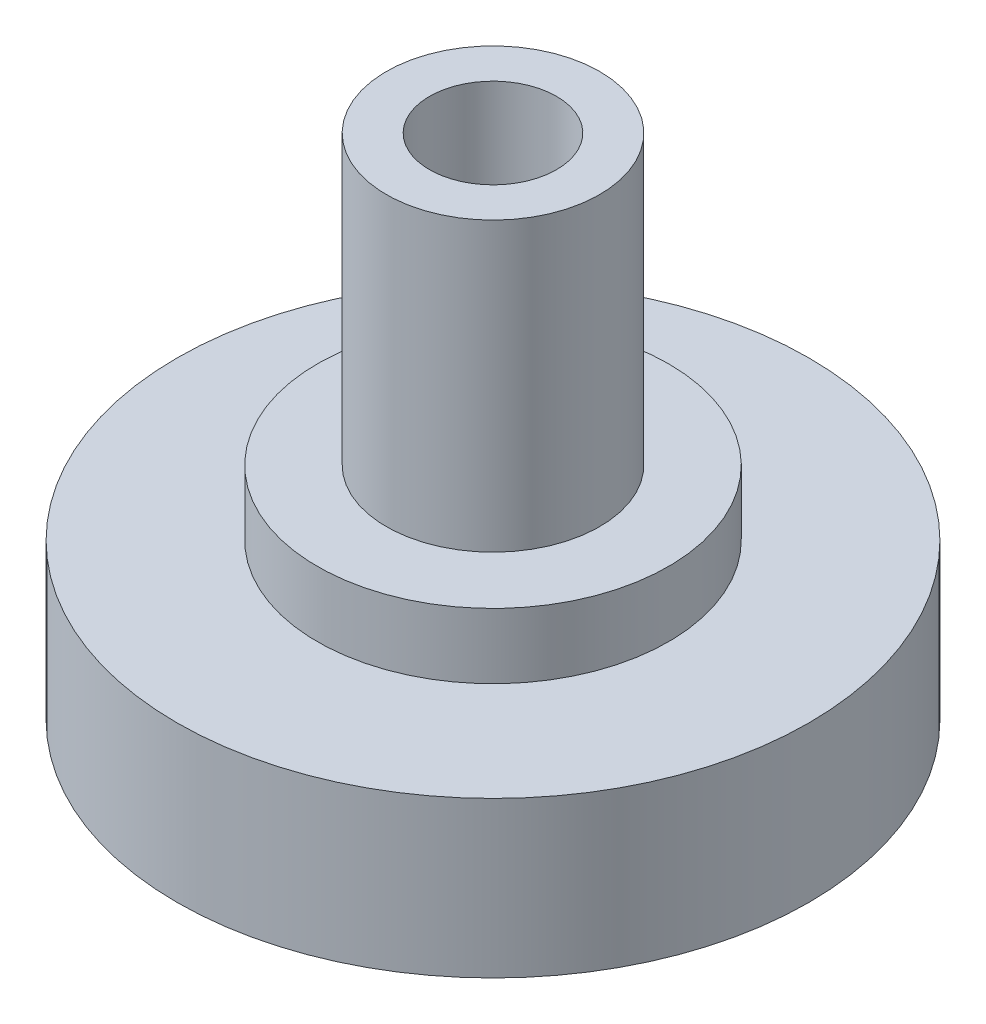
SolidWorks part; units mm, degrees
ref_plane "Front" through (0, 0, 0) normal (0, 0, 1) x (1, 0, 0)
ref_plane "Top" through (0, 0, 0) normal (0, 1, 0) x (1, 0, 0)
ref_plane "Right" through (0, 0, 0) normal (1, 0, 0) x (0, 0, -1)
sketch "Sketch1" plane through (0, 0, 0) normal (0, 0, 1) x (1, 0, 0)
  line L0 (0, 0) -> (0, 27.9526) construction
  line L1 (0, 0) -> (9.45, 0)
  line L2 (9.45, 0) -> (9.45, 4.65)
  line L3 (9.45, 4.65) -> (5.25, 4.65)
  line L4 (5.25, 4.65) -> (5.25, 6.6)
  line L5 (5.25, 6.6) -> (3.19, 6.6)
  line L6 (3.19, 6.6) -> (3.19, 15.2)
  line L7 (3.19, 15.2) -> (1.9, 15.2)
  line L8 (1.9, 15.2) -> (1.9, 10.2)
  line L9 (1.9, 10.2) -> (0, 10.2)
  line L10 (0, 10.2) -> (0, 0)
  dimension "D1" = 18.9
  dimension "D2" = 4.65
  dimension "D3" = 10.5
  dimension "D4" = 6.6
  dimension "D5" = 15.2
  dimension "D6" = 6.38
  dimension "D7" = 3.8
  dimension "D8" = 5
revolve "Revolve1" add sketch "Sketch1" angle 360 about L0
